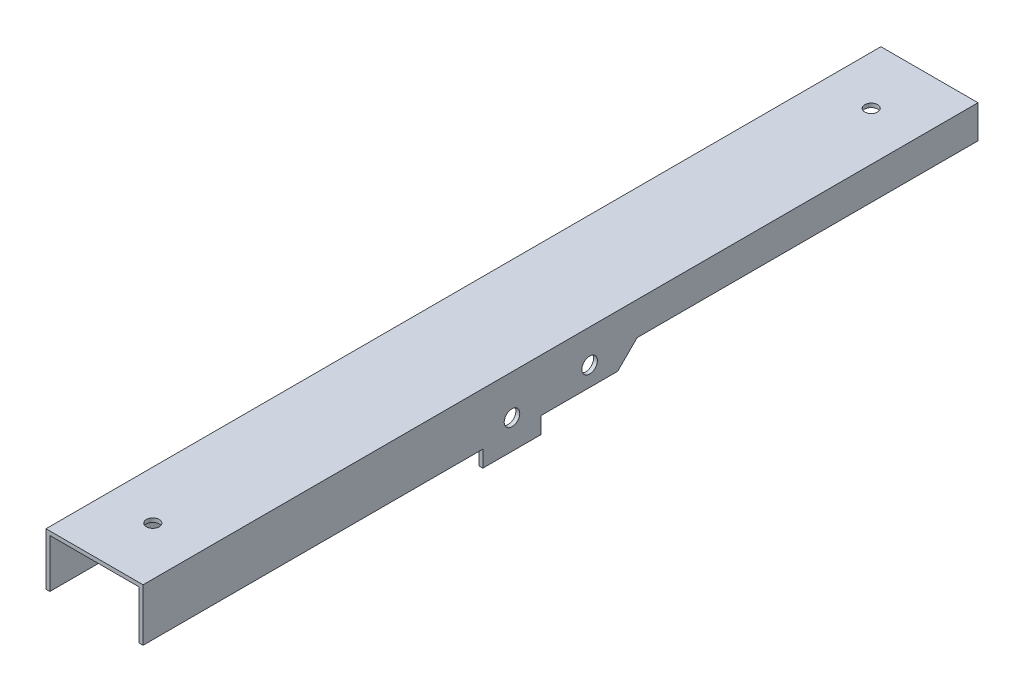
SolidWorks part; units mm, degrees
material "AISI 304"
ref_plane "Front Plane" through (0, 0, 0) normal (1, 0, 0) x (0, 1, 0)
ref_plane "Top Plane" through (0, 0, 0) normal (0, 0, 1) x (0, 1, 0)
ref_plane "Right Plane" through (0, 0, 0) normal (0, 1, 0) x (-1, 0, 0)
sketch "Sketch1" plane through (0, 0, 0) normal (1, 0, 0) x (0, 1, 0)
  line L0 (15, 230) -> (15, -200)
  line L1 (15, -200) -> (0, -200)
  line L2 (-10, -14.4374) -> (-10, 25)
  line L3 (-10, 25) -> (-18.4995, 25)
  line L4 (-18.4995, 25) -> (-18.4995, 55)
  line L5 (-18.4995, 55) -> (-10, 55)
  line L6 (-10, 55) -> (-10, 230)
  line L7 (-10, 230) -> (15, 230)
  line L8 (0, 0) -> (-3.4995, 40) construction
  line L9 (-10, -14.4374) -> (0, -24.4374)
  line L10 (0, -24.4374) -> (0, -200)
  circle A0 centre (0, 0) radius 4
  circle A1 centre (-3.4995, 40) radius 4
  point P13 (0, -33.0984)
  point P14 (-18.4995, 40)
  point P18 (0, 0)
  point P19 (0, 0)
  point P20 (-18.4995, -9.3481)
  point P21 (0, -20.4253)
  dimension "D1" = 8
  dimension "D5" = 8
  dimension "D2" = 430
  dimension "D3" = 200
  dimension "D4" = 5
  dimension "D6" = 40
  dimension "D7" = 15
  dimension "D8" = 10
  dimension "D9" = 15
  dimension "D10" = 15
  dimension "D11" = 45
extrude "Boss-Extrude1" add sketch "Sketch1" against normal blind 2
sketch "Sketch2" plane through (0, 15, 0) normal (0, 1, 0) x (-1, 0, 0)
  line L1 (0, 230) -> (25, 230)
  line L2 (0, 230) -> (0, -200)
  line L3 (0, -200) -> (25, -200)
  line L4 (25, 230) -> (25, -200)
  point P5 (0, 0)
  dimension "D1" = 25
extrude "Boss-Extrude2" add sketch "Sketch2" along normal blind 2
mirror "Mirror1" about plane through (-25, 17, 230) normal (1, 0, 0) of bodies 102
sketch "Sketch3" plane through (0, 17, 0) normal (0, 1, 0) x (-1, 0, 0)
  line L0 (50, 230) -> (0, 230) construction
  line L1 (0, -200) -> (50, -200) construction
  circle A0 centre (25, 200) radius 3.3
  circle A1 centre (25, -170) radius 3.3
  point P5 (25, 230)
  point P9 (25, -200)
  point P10 (0, 0)
  dimension "D1" = 6.6
  dimension "D2" = 30
  dimension "D3" = 30
extrude "Cut-Extrude1" cut sketch "Sketch3" against normal through all both and the other way through all
equation "\"D3@Sketch3\"=\"D2@Sketch3\""
